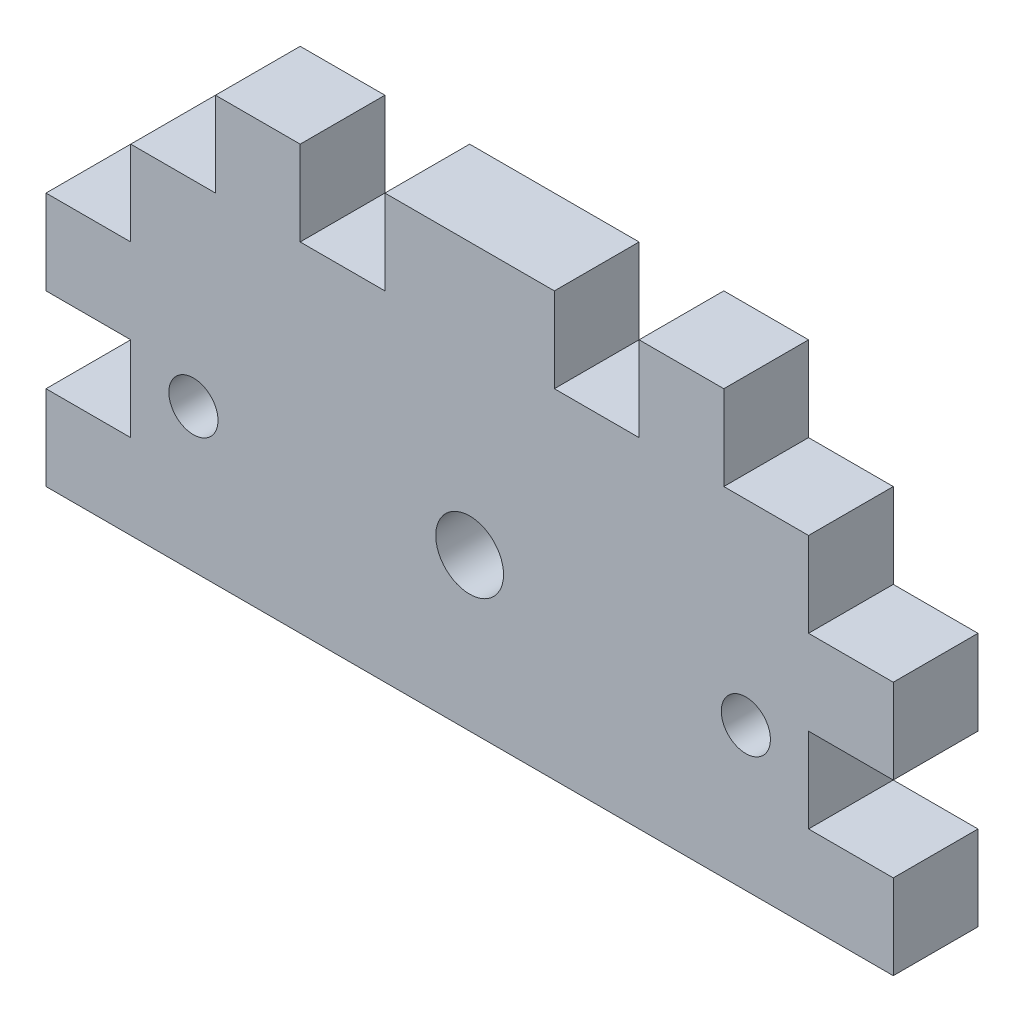
SolidWorks part; units mm, degrees
ref_plane "Plan de face" through (0, 0, 0) normal (0, 0, 1) x (1, 0, 0)
ref_plane "Plan de dessus" through (0, 0, 0) normal (0, 1, 0) x (1, 0, 0)
ref_plane "Plan de droite" through (0, 0, 0) normal (1, 0, 0) x (0, 0, -1)
sketch "Esquisse1" plane through (0, 0, 0) normal (0, 0, 1) x (1, 0, 0)
  line L1 (-66.0216, -12.9076) -> (-41.0216, -12.9076)
  line L2 (-66.0216, -12.9076) -> (-66.0216, -37.9076)
  line L3 (-66.0216, -37.9076) -> (-41.0216, -37.9076)
  line L4 (-41.0216, -12.9076) -> (-41.0216, -37.9076)
extrude "Boss.-Extru.1" add sketch "Esquisse1" along normal blind 5
sketch "Esquisse3" plane through (0, 0, 0) normal (0, 0, -1) x (-1, 0, 0)
  line L0 (41.0216, -12.9076) -> (66.0216, -12.9076) construction
  line L1 (46.0216, -22.9076) -> (46.0216, -17.9076)
  line L2 (66.0216, -37.9076) -> (41.0216, -37.9076) construction
  line L3 (51.0216, -12.9076) -> (41.0216, -12.9076)
  line L4 (41.0216, -32.9076) -> (46.0216, -32.9076)
  line L5 (41.0216, -12.9076) -> (41.0216, -22.9076)
  line L6 (41.0216, -32.9076) -> (41.0216, -27.9076)
  line L7 (41.0216, -37.9076) -> (41.0216, -12.9076) construction
  line L8 (41.0216, -22.9076) -> (46.0216, -22.9076)
  line L9 (46.0216, -17.9076) -> (51.0216, -17.9076)
  line L10 (51.0216, -17.9076) -> (51.0216, -12.9076)
  line L11 (61.0216, -12.9076) -> (56.0216, -12.9076)
  line L12 (61.0216, -12.9076) -> (61.0216, -17.9076)
  line L13 (61.0216, -17.9076) -> (56.0216, -17.9076)
  line L14 (56.0216, -12.9076) -> (56.0216, -17.9076)
  line L17 (41.0216, -27.9076) -> (46.0216, -27.9076)
  line L18 (46.0216, -32.9076) -> (46.0216, -27.9076)
  circle A0 centre (49.7216, -29.4576) radius 1.45
  dimension "D8" = 8.7
  dimension "D1" = 5
  dimension "D5" = 5
  dimension "D7" = 8.45
extrude "Enlèv. mat.-Extru.1" cut sketch "Esquisse3" against normal blind 5
mirror "Symétrie1" about plane through (-66.0216, -12.9076, 5) normal (1, 0, 0) of "Enlèv. mat.-Extru.1", "Boss.-Extru.1"
sketch "Esquisse5" plane through (0, 0, 5) normal (0, 0, 1) x (1, 0, 0)
  line L0 (-91.0216, -37.9076) -> (-41.0216, -37.9076) construction
  line L1 (-86.0216, -32.9076) -> (-86.0216, -27.9076) construction
  circle A0 centre (-66.0216, -28.9076) radius 2
  point P2 (-66.0216, -37.9076)
  dimension "D1" = 4
  dimension "D2" = 9
  dimension "D3" = 20
extrude "Enlèv. mat.-Extru.2" cut sketch "Esquisse5" against normal blind 10
